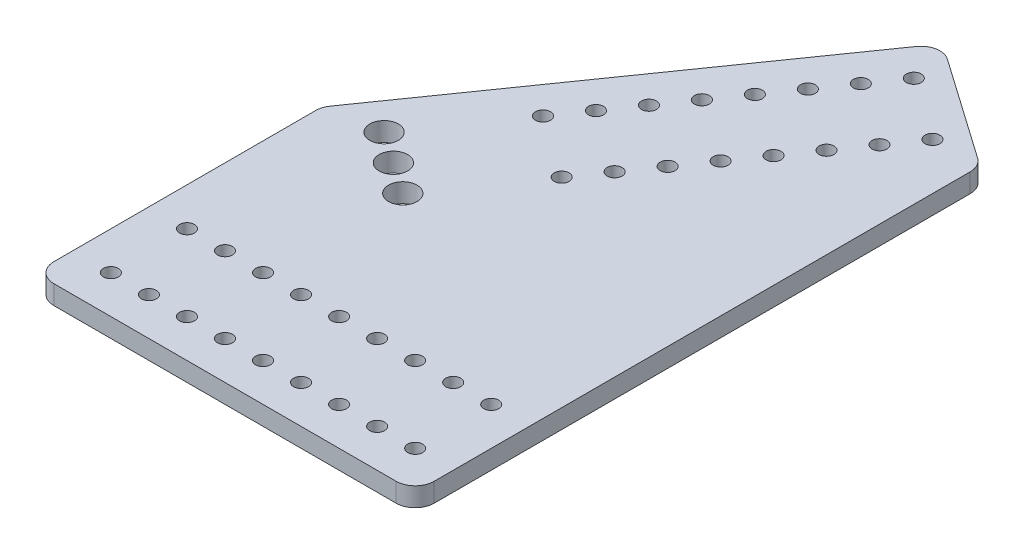
SolidWorks part; units mm, degrees
material "6061-T6 (SS)"
ref_plane "Front Plane" through (0, 0, 0) normal (0, 0, 1) x (1, 0, 0)
ref_plane "Top Plane" through (0, 0, 0) normal (0, 1, 0) x (1, 0, 0)
ref_plane "Right Plane" through (0, 0, 0) normal (1, 0, 0) x (0, 0, -1)
sketch "Sketch1" plane through (0, 0, 0) normal (0, 1, 0) x (1, 0, 0)
  line L0 (0, 95.8127) -> (85.3871, 217.7581)
  line L5 (0, 0) -> (127, 0)
  line L6 (0, 0) -> (0, 95.8127)
  line L7 (85.3871, 217.7581) -> (127, 217.7581) construction
  line L8 (127, 0) -> (127, 188.6204)
  line L9 (85.3871, 217.7581) -> (127, 188.6204)
  line L10 (127, 188.6204) -> (127, 217.7581) construction
  line L11 (0, 0) -> (-12.7, 0) construction
  line L12 (-12.7, 0) -> (-12.7, 77.6752) construction
  line L13 (0, 95.8127) -> (41.6129, 66.675) construction
  line L14 (0, 95.8127) -> (85.3871, 217.7581) construction
  line L15 (41.6129, 66.675) -> (127, 188.6204) construction
  line L16 (85.3871, 217.7581) -> (127, 188.6204) construction
  dimension "D1" = 66.675
  dimension "D2" = 127
  dimension "D3" = 55
  dimension "D4" = 50.8
  dimension "D5" = 12.7
  dimension "D6" = 12.7
extrude "Boss-Extrude1" add sketch "Sketch1" along normal blind 6.35
sketch "Sketch2" plane through (0, 6.35, 0) normal (0, 1, 0) x (1, 0, 0)
  line L0 (0, 0) -> (127, 0) construction
  line L1 (0, 95.8127) -> (0, 0) construction
  line L2 (90.5319, 202.9638) -> (111.3383, 188.395) construction
  line L3 (127, 188.6204) -> (85.3871, 217.7581) construction
  line L4 (85.3871, 217.7581) -> (0, 95.8127) construction
  line L5 (17.6877, 98.9315) -> (38.4941, 84.3627) construction
  line L6 (38.4941, 84.3627) -> (60.3474, 115.5723) construction
  line L7 (0, 95.8127) -> (41.6129, 66.675) construction
  line L8 (0, 95.8127) -> (85.3871, 217.7581) construction
  line L9 (41.6129, 66.675) -> (127, 188.6204) construction
  line L10 (85.3871, 217.7581) -> (127, 188.6204) construction
  circle A0 centre (12.7, 12.7) radius 2.4892
  circle A2 centre (12.7, 38.1) radius 2.4892
  circle A3 centre (25.4, 38.1) radius 2.4892
  circle A4 centre (38.1, 38.1) radius 2.4892
  circle A5 centre (50.8, 38.1) radius 2.4892
  circle A6 centre (63.5, 38.1) radius 2.4892
  circle A7 centre (25.4, 12.7) radius 2.4892
  circle A8 centre (38.1, 12.7) radius 2.4892
  circle A9 centre (50.8, 12.7) radius 2.4892
  circle A10 centre (63.5, 12.7) radius 2.4892
  circle A11 centre (76.2, 12.7) radius 2.4892
  circle A12 centre (76.2, 38.1) radius 2.4892
  circle A13 centre (88.9, 12.7) radius 2.4892
  circle A14 centre (88.9, 38.1) radius 2.4892
  circle A15 centre (101.6, 12.7) radius 2.4892
  circle A16 centre (101.6, 38.1) radius 2.4892
  circle A21 centre (90.5319, 202.9638) radius 2.4892
  circle A22 centre (111.3383, 188.395) radius 2.4892
  circle A23 centre (83.2474, 192.5606) radius 2.4892
  circle A24 centre (104.0539, 177.9917) radius 2.4892
  circle A25 centre (75.963, 182.1573) radius 2.4892
  circle A26 centre (96.7695, 167.5885) radius 2.4892
  circle A27 centre (68.6786, 171.7541) radius 2.4892
  circle A28 centre (89.4851, 157.1853) radius 2.4892
  circle A29 centre (61.3942, 161.3509) radius 2.4892
  circle A30 centre (82.2006, 146.782) radius 2.4892
  circle A31 centre (54.1098, 150.9476) radius 2.4892
  circle A32 centre (74.9162, 136.3788) radius 2.4892
  circle A33 centre (46.8253, 140.5444) radius 2.4892
  circle A34 centre (67.6318, 125.9756) radius 2.4892
  circle A35 centre (39.5409, 130.1412) radius 2.4892
  circle A36 centre (60.3474, 115.5723) radius 2.4892
  circle A37 centre (17.6877, 98.9315) radius 4.7625
  circle A38 centre (28.0909, 91.6471) radius 4.7625
  circle A39 centre (38.4941, 84.3627) radius 4.7625
  circle A40 centre (114.3, 12.7) radius 2.4892
  circle A41 centre (114.3, 38.1) radius 2.4892
  dimension "D1" = 4.9784
  dimension "D2" = 12.7
  dimension "D3" = 12.7
  dimension "D6" = 25.4
  dimension "D7" = 12.7
  dimension "D8" = 50.8
  dimension "D9" = 4.9784
  dimension "D15" = 9.525
  dimension "D10" = 12.7
  dimension "D11" = 25.4
  dimension "D12" = 12.7
  dimension "D13" = 8
  dimension "D16" = 50.8
  dimension "D17" = 12.7
  dimension "D4" = 2
  dimension "D5" = 9
extrude "Cut-Extrude1" cut sketch "Sketch2" against normal through all
fillet "Fillet1" radius 6.35 5 edges at (85.3871, 3.175, -217.7581) (127, 3.175, -188.6204) (127, 3.175, 0) (0, 3.175, 0) (0, 3.175, -95.8127)
